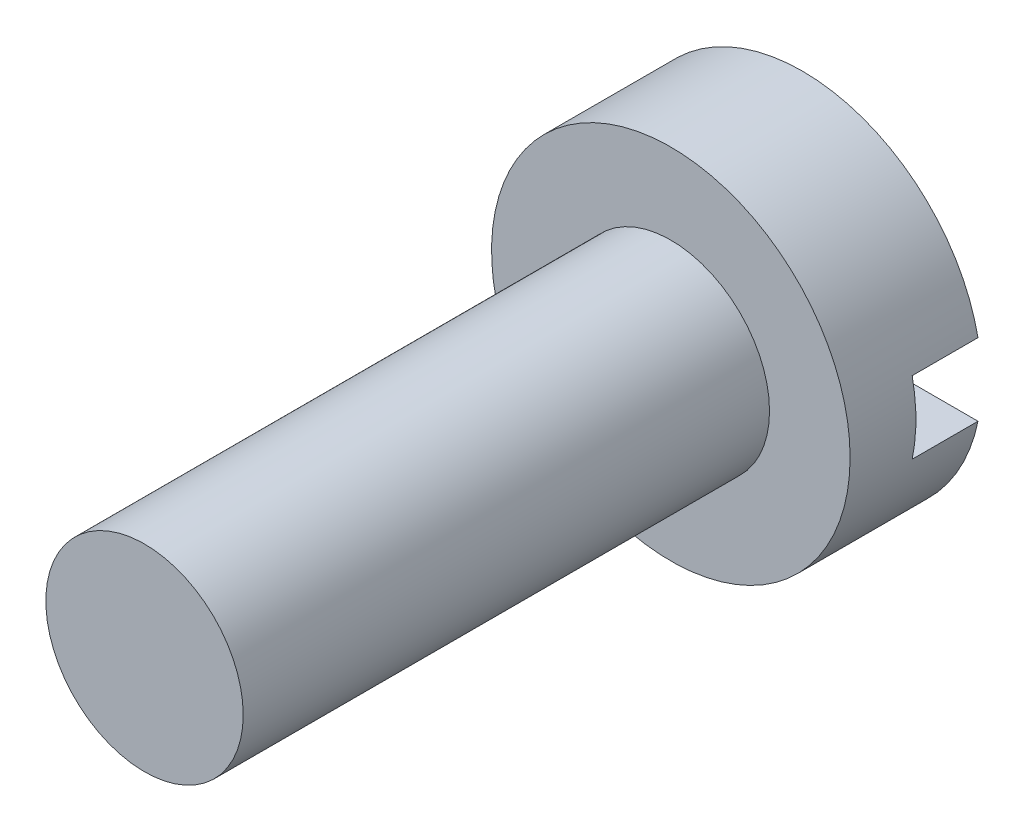
SolidWorks part; units mm, degrees
ref_plane "Front Plane" through (0, 0, 0) normal (0, 0, 1) x (1, 0, 0)
ref_plane "Top Plane" through (0, 0, 0) normal (0, 1, 0) x (1, 0, 0)
ref_plane "Right Plane" through (0, 0, 0) normal (1, 0, 0) x (0, 0, -1)
sketch "Sketch1" plane through (0, 0, 0) normal (0, 0, 1) x (1, 0, 0)
  circle A0 centre (0, 0) radius 2.725
extrude "Extrude1" add sketch "Sketch1" along normal blind 2
sketch "Sketch2" plane through (0, 0, 0) normal (0, 0, -1) x (-1, 0, 0)
  line L0 (-3.9013, 0) -> (3.4498, 0) construction
  line L1 (3.4498, 0) -> (3.4498, 0.55)
  line L2 (3.4498, 0.55) -> (-3.9013, 0.55)
  line L3 (-3.9013, 0.55) -> (-3.9013, -0.55)
  line L4 (-3.9013, -0.55) -> (3.4498, -0.55)
  line L5 (3.4498, -0.55) -> (3.4498, 0)
extrude "Cut-Extrude1" cut sketch "Sketch2" against normal blind 1
sketch "Sketch3" plane through (0, 0, 2) normal (0, 0, 1) x (1, 0, 0)
  circle A0 centre (0, 0) radius 1.5
extrude "Extrude2" add sketch "Sketch3" along normal blind 8
